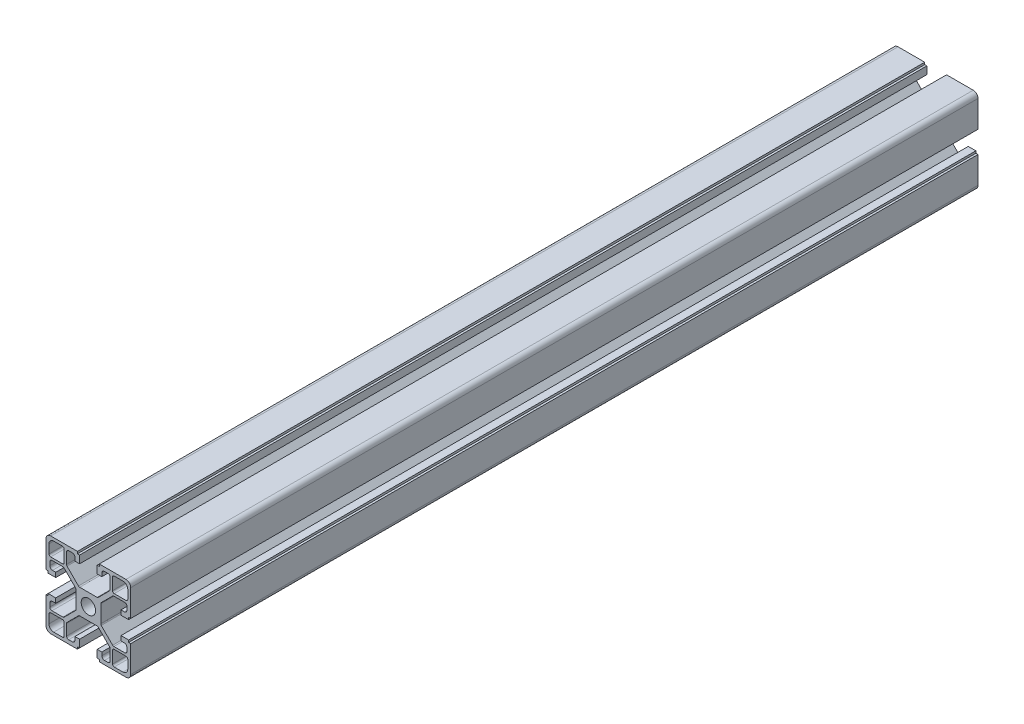
SolidWorks part; units mm, degrees
material "6063-T5"
ref_plane "Front Plane" through (0, 0, 0) normal (0, 0, 1) x (1, 0, 0)
ref_plane "Top Plane" through (0, 0, 0) normal (0, 1, 0) x (1, 0, 0)
ref_plane "Right Plane" through (0, 0, 0) normal (1, 0, 0) x (0, 0, -1)
sketch "Sketch1" plane through (0, 0, 0) normal (0, 0, 1) x (1, 0, 0)
  line L4 (20, 17.75) -> (20, 5.15)
  line L5 (0, -17.7813) -> (0, 18.2) construction
  line L6 (0, 0) -> (38.8613, 0) construction
  line L8 (18.6, 16.35) -> (18.6, 12.2)
  line L10 (11.4, 17.8) -> (11.4, 12.2)
  line L11 (-4.1, 5.85) -> (4.1, 5.85)
  line L14 (5.85, 4.1089) -> (5.85, -4.1089)
  line L17 (12.2, 11.4) -> (17.8, 11.4)
  line L24 (4.15, 19) -> (4.15, 15.4)
  line L25 (4.15, 15.4) -> (6.35, 15.4)
  line L26 (6.35, 15.4) -> (6.35, 16.95)
  line L27 (10.3, 17.2) -> (10.3, 12.0545)
  line L28 (10.0659, 11.489) -> (4.6659, 6.0845)
  line L29 (6.0841, 4.6743) -> (11.4708, 10.0655)
  line L30 (12.0367, 10.3) -> (17.2, 10.3)
  line L31 (18.2, 9.3) -> (18.2, 7.6)
  line L32 (16.95, 6.35) -> (15.4, 6.35)
  line L33 (15.4, 6.35) -> (15.4, 4.15)
  line L34 (15.4, 4.15) -> (19, 4.15)
  line L35 (18.6, 18.6) -> (18.6, -18.6) construction
  line L36 (-18.6, 18.6) -> (18.6, 18.6) construction
  line L37 (-20, 20) -> (20, 20) construction
  line L38 (20, 20) -> (20, -20) construction
  line L40 (7.6, 18.2) -> (9.3, 18.2)
  line L42 (4.15, 19) -> (5.15, 19)
  line L43 (5.15, 19) -> (5.15, 20)
  line L56 (-18.6, 18.6) -> (-18.6, -18.6) construction
  line L57 (-20, 20) -> (-20, -20) construction
  line L60 (5.15, 20) -> (17.75, 20)
  line L91 (-18.6, -18.6) -> (18.6, -18.6) construction
  line L92 (-20, -20) -> (20, -20) construction
  line L93 (12.2, 18.6) -> (16.35, 18.6)
  line L94 (17.9399, 17.9421) -> (20, 20) construction
  line L95 (0, 0) -> (11.4, 11.4094) construction
  line L101 (19, 4.15) -> (19, 5.15)
  line L102 (19, 5.15) -> (20, 5.15)
  line L104 (-5.85, 4.1089) -> (-5.85, -4.1089)
  line L105 (-19, 5.15) -> (-20, 5.15)
  line L106 (-19, 4.15) -> (-19, 5.15)
  line L107 (-12.2, 18.6) -> (-16.35, 18.6)
  line L108 (-5.15, 20) -> (-17.75, 20)
  line L109 (-5.15, 19) -> (-5.15, 20)
  line L110 (-4.15, 19) -> (-5.15, 19)
  line L111 (-7.6, 18.2) -> (-9.3, 18.2)
  line L112 (-15.4, 4.15) -> (-19, 4.15)
  line L113 (-15.4, 6.35) -> (-15.4, 4.15)
  line L114 (-16.95, 6.35) -> (-15.4, 6.35)
  line L115 (-18.2, 9.3) -> (-18.2, 7.6)
  line L116 (-12.0367, 10.3) -> (-17.2, 10.3)
  line L117 (-6.0841, 4.6743) -> (-11.4708, 10.0655)
  line L118 (-10.0659, 11.489) -> (-4.6659, 6.0845)
  line L119 (-10.3, 17.2) -> (-10.3, 12.0545)
  line L120 (-6.35, 15.4) -> (-6.35, 16.95)
  line L121 (-4.15, 15.4) -> (-6.35, 15.4)
  line L122 (-4.15, 19) -> (-4.15, 15.4)
  line L123 (-12.2, 11.4) -> (-17.8, 11.4)
  line L124 (-11.4, 17.8) -> (-11.4, 12.2)
  line L125 (-18.6, 16.35) -> (-18.6, 12.2)
  line L126 (-20, 17.75) -> (-20, 5.15)
  line L127 (-20, -17.75) -> (-20, -5.15)
  line L128 (-18.6, -16.35) -> (-18.6, -12.2)
  line L129 (-11.4, -17.8) -> (-11.4, -12.2)
  line L130 (-12.2, -11.4) -> (-17.8, -11.4)
  line L131 (-4.15, -19) -> (-4.15, -15.4)
  line L132 (-4.15, -15.4) -> (-6.35, -15.4)
  line L133 (-6.35, -15.4) -> (-6.35, -16.95)
  line L134 (-10.3, -17.2) -> (-10.3, -12.0545)
  line L135 (-10.0659, -11.489) -> (-4.6659, -6.0845)
  line L136 (-6.0841, -4.6743) -> (-11.4708, -10.0655)
  line L137 (-12.0367, -10.3) -> (-17.2, -10.3)
  line L138 (-18.2, -9.3) -> (-18.2, -7.6)
  line L139 (-16.95, -6.35) -> (-15.4, -6.35)
  line L140 (-15.4, -6.35) -> (-15.4, -4.15)
  line L141 (-15.4, -4.15) -> (-19, -4.15)
  line L142 (-7.6, -18.2) -> (-9.3, -18.2)
  line L143 (-4.15, -19) -> (-5.15, -19)
  line L144 (-5.15, -19) -> (-5.15, -20)
  line L145 (-5.15, -20) -> (-17.75, -20)
  line L146 (-12.2, -18.6) -> (-16.35, -18.6)
  line L147 (-19, -4.15) -> (-19, -5.15)
  line L148 (-19, -5.15) -> (-20, -5.15)
  line L149 (19, -5.15) -> (20, -5.15)
  line L150 (19, -4.15) -> (19, -5.15)
  line L151 (12.2, -18.6) -> (16.35, -18.6)
  line L152 (5.15, -20) -> (17.75, -20)
  line L153 (5.15, -19) -> (5.15, -20)
  line L154 (4.15, -19) -> (5.15, -19)
  line L155 (7.6, -18.2) -> (9.3, -18.2)
  line L156 (15.4, -4.15) -> (19, -4.15)
  line L157 (15.4, -6.35) -> (15.4, -4.15)
  line L158 (16.95, -6.35) -> (15.4, -6.35)
  line L159 (18.2, -9.3) -> (18.2, -7.6)
  line L160 (12.0367, -10.3) -> (17.2, -10.3)
  line L161 (6.0841, -4.6743) -> (11.4708, -10.0655)
  line L162 (10.0659, -11.489) -> (4.6659, -6.0845)
  line L163 (10.3, -17.2) -> (10.3, -12.0545)
  line L164 (6.35, -15.4) -> (6.35, -16.95)
  line L165 (4.15, -15.4) -> (6.35, -15.4)
  line L166 (4.15, -19) -> (4.15, -15.4)
  line L167 (12.2, -11.4) -> (17.8, -11.4)
  line L168 (-4.1, -5.85) -> (4.1, -5.85)
  line L169 (11.4, -17.8) -> (11.4, -12.2)
  line L170 (18.6, -16.35) -> (18.6, -12.2)
  line L171 (20, -17.75) -> (20, -5.15)
  circle A0 centre (0, 0) radius 3.4
  arc A7 (16.35, 18.6) -> (18.6, 16.35) centre (16.35, 16.35) cw
  arc A8 (20, 17.75) -> (17.75, 20) centre (17.75, 17.75) ccw
  arc A9 (6.35, 16.95) -> (7.6, 18.2) centre (7.6, 16.95) cw
  arc A10 (18.2, 7.6) -> (16.95, 6.35) centre (16.95, 7.6) cw
  arc A11 (17.2, 10.3) -> (18.2, 9.3) centre (17.2, 9.3) cw
  arc A12 (9.3, 18.2) -> (10.3, 17.2) centre (9.3, 17.2) cw
  arc A13 (4.6659, 6.0845) -> (4.1, 5.85) centre (4.1, 6.65) cw
  arc A14 (6.0841, 4.6743) -> (5.85, 4.1089) centre (6.65, 4.1089) ccw
  arc A15 (17.8, 11.4) -> (18.6, 12.2) centre (17.8, 12.2) ccw
  arc A16 (12.2, 18.6) -> (11.4, 17.8) centre (12.2, 17.8) ccw
  arc A17 (11.4, 12.2) -> (12.2, 11.4) centre (12.2, 12.2) ccw
  arc A18 (11.4708, 10.0655) -> (12.0367, 10.3) centre (12.0367, 9.5) cw
  arc A19 (10.3, 12.0545) -> (10.0659, 11.489) centre (9.5, 12.0545) cw
  arc A20 (-10.3, 12.0545) -> (-10.0659, 11.489) centre (-9.5, 12.0545) ccw
  arc A21 (-11.4708, 10.0655) -> (-12.0367, 10.3) centre (-12.0367, 9.5) ccw
  arc A22 (-11.4, 12.2) -> (-12.2, 11.4) centre (-12.2, 12.2) cw
  arc A23 (-12.2, 18.6) -> (-11.4, 17.8) centre (-12.2, 17.8) cw
  arc A24 (-17.8, 11.4) -> (-18.6, 12.2) centre (-17.8, 12.2) cw
  arc A25 (-6.0841, 4.6743) -> (-5.85, 4.1089) centre (-6.65, 4.1089) cw
  arc A26 (-4.6659, 6.0845) -> (-4.1, 5.85) centre (-4.1, 6.65) ccw
  arc A27 (-9.3, 18.2) -> (-10.3, 17.2) centre (-9.3, 17.2) ccw
  arc A28 (-17.2, 10.3) -> (-18.2, 9.3) centre (-17.2, 9.3) ccw
  arc A29 (-18.2, 7.6) -> (-16.95, 6.35) centre (-16.95, 7.6) ccw
  arc A30 (-6.35, 16.95) -> (-7.6, 18.2) centre (-7.6, 16.95) ccw
  arc A31 (-20, 17.75) -> (-17.75, 20) centre (-17.75, 17.75) cw
  arc A32 (-16.35, 18.6) -> (-18.6, 16.35) centre (-16.35, 16.35) ccw
  arc A33 (-16.35, -18.6) -> (-18.6, -16.35) centre (-16.35, -16.35) cw
  arc A34 (-20, -17.75) -> (-17.75, -20) centre (-17.75, -17.75) ccw
  arc A35 (-6.35, -16.95) -> (-7.6, -18.2) centre (-7.6, -16.95) cw
  arc A36 (-18.2, -7.6) -> (-16.95, -6.35) centre (-16.95, -7.6) cw
  arc A37 (-17.2, -10.3) -> (-18.2, -9.3) centre (-17.2, -9.3) cw
  arc A38 (-9.3, -18.2) -> (-10.3, -17.2) centre (-9.3, -17.2) cw
  arc A39 (-4.6659, -6.0845) -> (-4.1, -5.85) centre (-4.1, -6.65) cw
  arc A40 (-6.0841, -4.6743) -> (-5.85, -4.1089) centre (-6.65, -4.1089) ccw
  arc A41 (-17.8, -11.4) -> (-18.6, -12.2) centre (-17.8, -12.2) ccw
  arc A42 (-12.2, -18.6) -> (-11.4, -17.8) centre (-12.2, -17.8) ccw
  arc A43 (-11.4, -12.2) -> (-12.2, -11.4) centre (-12.2, -12.2) ccw
  arc A44 (-11.4708, -10.0655) -> (-12.0367, -10.3) centre (-12.0367, -9.5) cw
  arc A45 (-10.3, -12.0545) -> (-10.0659, -11.489) centre (-9.5, -12.0545) cw
  arc A46 (10.3, -12.0545) -> (10.0659, -11.489) centre (9.5, -12.0545) ccw
  arc A47 (11.4708, -10.0655) -> (12.0367, -10.3) centre (12.0367, -9.5) ccw
  arc A48 (11.4, -12.2) -> (12.2, -11.4) centre (12.2, -12.2) cw
  arc A49 (12.2, -18.6) -> (11.4, -17.8) centre (12.2, -17.8) cw
  arc A50 (17.8, -11.4) -> (18.6, -12.2) centre (17.8, -12.2) cw
  arc A51 (6.0841, -4.6743) -> (5.85, -4.1089) centre (6.65, -4.1089) cw
  arc A52 (4.6659, -6.0845) -> (4.1, -5.85) centre (4.1, -6.65) ccw
  arc A53 (9.3, -18.2) -> (10.3, -17.2) centre (9.3, -17.2) ccw
  arc A54 (17.2, -10.3) -> (18.2, -9.3) centre (17.2, -9.3) ccw
  arc A55 (18.2, -7.6) -> (16.95, -6.35) centre (16.95, -7.6) ccw
  arc A56 (6.35, -16.95) -> (7.6, -18.2) centre (7.6, -16.95) ccw
  arc A57 (20, -17.75) -> (17.75, -20) centre (17.75, -17.75) cw
  arc A58 (16.35, -18.6) -> (18.6, -16.35) centre (16.35, -16.35) ccw
  point P0 (0, 0)
  point P16 (-5.85, 0)
  point P66 (0, 5.85)
  point P120 (5.85, 0)
  point P218 (0, -5.85)
  dimension "D5" = 6.8
  dimension "D6" = 1.4
  dimension "D15" = 5.85
  dimension "D44" = 2.25
  dimension "D25" = 1.25
  dimension "D26" = 1
  dimension "D27" = 0.8
  dimension "D7" = 1.1
  dimension "D8" = 1.1
  dimension "D9" = 1.8
  dimension "D10" = 2.2
  dimension "D11" = 4.6
  dimension "D12" = 1.8
  dimension "D13" = 2.2
  dimension "D14" = 5.85
  dimension "D16" = 1.4
  dimension "D17" = 4.15
  dimension "D18" = 1
  dimension "D19" = 1
  dimension "D20" = 10.3
  dimension "D21" = 4.15
  dimension "D22" = 2
  dimension "D23" = 45.024
  dimension "D24" = 1
  dimension "D41" = 10.3
  dimension "D60" = 14.15
  dimension "D73" = 1
  dimension "D74" = 1
  dimension "D82" = 14.15
  dimension "D3" = 4.6
extrude "Boss-Extrude1" add sketch "Sketch1" along normal blind 400
